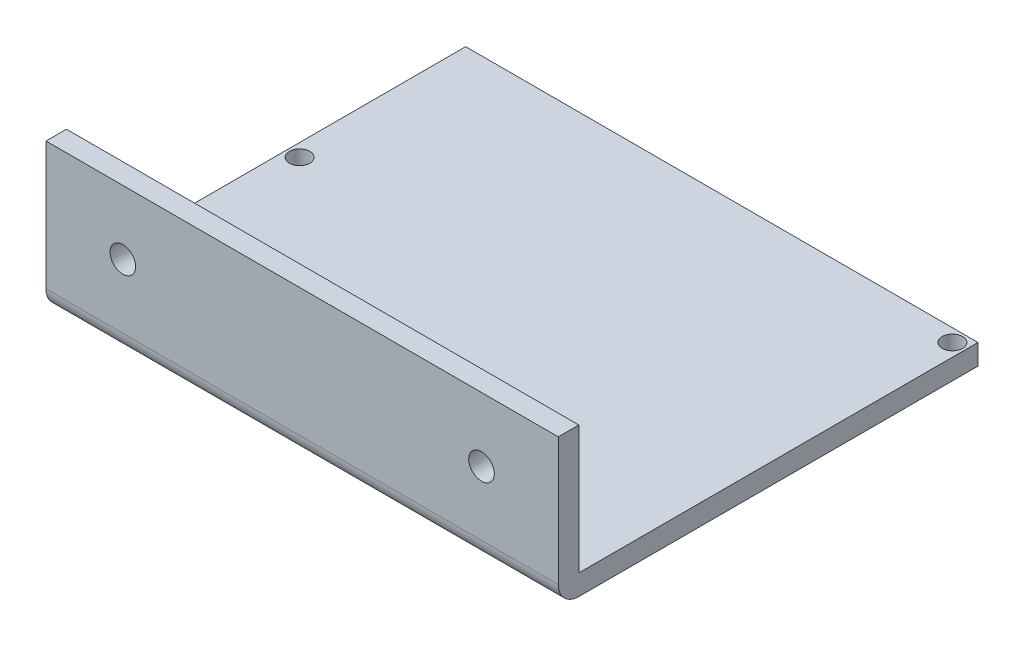
SolidWorks part; units mm, degrees
ref_plane "Front Plane" through (0, 0, 0) normal (0, 0, 1) x (1, 0, 0)
ref_plane "Top Plane" through (0, 0, 0) normal (0, 1, 0) x (1, 0, 0)
ref_plane "Right Plane" through (0, 0, 0) normal (1, 0, 0) x (0, 0, -1)
sketch "Sketch1" plane through (0, 0, 0) normal (0, 1, 0) x (1, 0, 0)
  line L0 (0, 0) -> (0, 72.9078)
  line L1 (0, 72.9078) -> (100, 72.9078)
  line L2 (100, 72.9078) -> (100, 0)
  line L3 (100, 0) -> (0, 0)
  line L4 (0, 0) -> (20, 0) construction
  line L5 (20, 0) -> (20, 3.5) construction
  line L6 (100, 0) -> (82.5, 0) construction
  line L7 (82.5, 0) -> (82.5, 3.5) construction
  line L8 (0, 0) -> (0, 38) construction
  line L9 (0, 38) -> (2.5, 38) construction
  line L10 (100, 72.9078) -> (97.5, 72.9078) construction
  line L11 (97.5, 72.9078) -> (97.5, 70.4078) construction
  circle A0 centre (20, 3.5) radius 2.0831
  circle A1 centre (82.5, 3.5) radius 2
  circle A2 centre (2.5, 38) radius 2
  circle A3 centre (97.5, 70.4078) radius 2
  dimension "D1" = 17.5
  dimension "D3" = 3.5
  dimension "D2" = 100
  dimension "D4" = 3.5
  dimension "D5" = 20
extrude "Boss-Extrude1" add sketch "Sketch1" along normal blind 4 contours L3 L2 L1 L0 A3 A2 A1 A0
sketch "Sketch2" plane through (0, 0, 0) normal (-1, 0, 0) x (0, 0, 1)
  line L0 (0, 4) -> (5, 4)
  line L1 (5, 4) -> (5, 29)
  line L2 (5, 29) -> (9, 29)
  line L3 (9, 29) -> (9, 5.3852)
  line L4 (9, 5.3852) -> (9, 4)
  line L5 (5, 0) -> (0, 0)
  line L6 (0, 0) -> (0, 4)
  arc A0 (9, 4) -> (5, 0) centre (5, 4) cw
  dimension "D1" = 5
  dimension "D2" = 25
  dimension "D3" = 4
extrude "Boss-Extrude2" add sketch "Sketch2" against normal up to surface (100 mm away) up to face at (100, 2, -36.4539)
sketch "Sketch3" plane through (0, 0, 9) normal (0, 0, 1) x (1, 0, 0)
  line L0 (0, 16.5) -> (15, 16.5) construction
  line L1 (0, 4) -> (0, 29) construction
  line L2 (15, 16.5) -> (100, 16.5) construction
  line L3 (100, 4) -> (100, 29) construction
  line L4 (100, 16.5) -> (85, 16.5) construction
  circle A0 centre (15, 16.5) radius 2.5
  circle A1 centre (85, 16.5) radius 2.5
  dimension "D1" = 15
  dimension "D2" = 15
extrude "Cut-Extrude1" cut sketch "Sketch3" against normal blind 4
sketch "Sketch4" plane through (0, 0, 0) normal (0, -1, 0) x (1, 0, 0)
  line L0 (51.9501, -63.6311) -> (12.6476, -63.6311)
  line L1 (91.2525, -70.9078) -> (12.6476, -70.9078)
  line L3 (91.2525, -63.6311) -> (61.9788, -63.6311)
  line L5 (78.4582, -5.6598) -> (24.4257, -5.6598)
  line L6 (78.4582, -5.6598) -> (78.4582, -1.4215)
  line L7 (78.4582, -1.4215) -> (24.4257, -1.4215)
  line L8 (24.4257, -5.6598) -> (24.4257, -1.4215)
  line L9 (12.6476, -70.9078) -> (3.433, -70.9078)
  line L10 (12.6476, -63.6311) -> (12.6476, -44.2809)
  line L11 (12.6476, -44.2809) -> (3.433, -44.2809)
  line L12 (3.433, -70.9078) -> (3.433, -44.2809)
  line L14 (91.2525, -63.6311) -> (91.2525, -36.4152)
  line L15 (91.2525, -36.4152) -> (97.8928, -36.4152)
  line L16 (97.8928, -63.6311) -> (97.8928, -36.4152)
  line L17 (16.3358, -5.6598) -> (3.433, -5.6598)
  line L18 (16.3358, -5.6598) -> (16.3358, -1.4215)
  line L19 (16.3358, -1.4215) -> (3.433, -1.4215)
  line L20 (3.433, -5.6598) -> (3.433, -1.4215)
  line L22 (61.9788, -63.6311) -> (61.9788, -54.7475)
  line L23 (61.9788, -54.7475) -> (51.9501, -54.7475)
  line L24 (51.9501, -63.6311) -> (51.9501, -54.7475)
  line L25 (91.2525, -70.9078) -> (97.8928, -63.6311)
  line L26 (0, -72.9078) -> (100, -72.9078) construction
  line L27 (100, -72.9078) -> (100, 5) construction
  dimension "D1" = 2
  dimension "D2" = 38.0212
extrude "Cut-Extrude4" cut sketch "Sketch4" against normal blind 2
